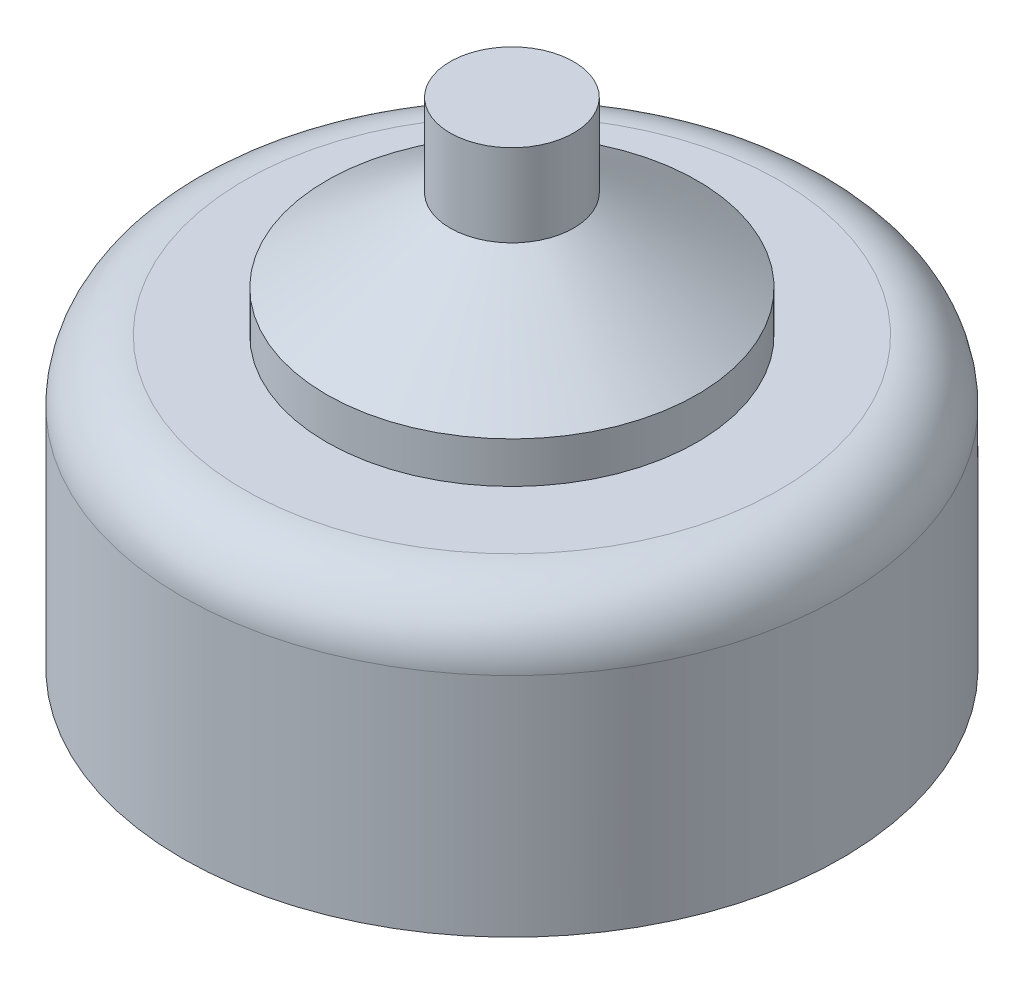
SolidWorks part; units mm, degrees
ref_plane "Front Plane" through (0, 0, 0) normal (0, 0, 1) x (1, 0, 0)
ref_plane "Top Plane" through (0, 0, 0) normal (0, 1, 0) x (1, 0, 0)
ref_plane "Right Plane" through (0, 0, 0) normal (1, 0, 0) x (0, 0, -1)
sketch "Sketch2" plane through (0, 0, 0) normal (0, 0, 1) x (1, 0, 0)
  line L0 (0, 46.0762) -> (0, -20.015) construction
  line L1 (0, -30.015) -> (8, -30.015)
  line L3 (8, -23.015) -> (4.5, -23.015)
  line L4 (4.5, -23.015) -> (4.5, -22.015)
  line L5 (4.5, -22.015) -> (1.5, -20.015)
  line L11 (8, -23.015) -> (8, -30.015)
  line L12 (1.5, -20.015) -> (1.5, -18.015)
  line L13 (1.5, -18.015) -> (0, -18.015)
  line L14 (0, -18.015) -> (0, -30.015)
  dimension "D1" = 10
  dimension "D2" = 7
revolve "Revolve1" add sketch "Sketch2" angle 360 about L0
fillet "Fillet2" radius 1.5 1 edges at (0, -23.015, 8)
sketch "Sketch3" plane through (0, -30.015, 0) normal (0, -1, 0) x (1, 0, 0)
  circle A0 centre (0, 0) radius 2
  dimension "D1" = 4
extrude "Boss-Extrude1" add sketch "Sketch3" along normal blind 3
